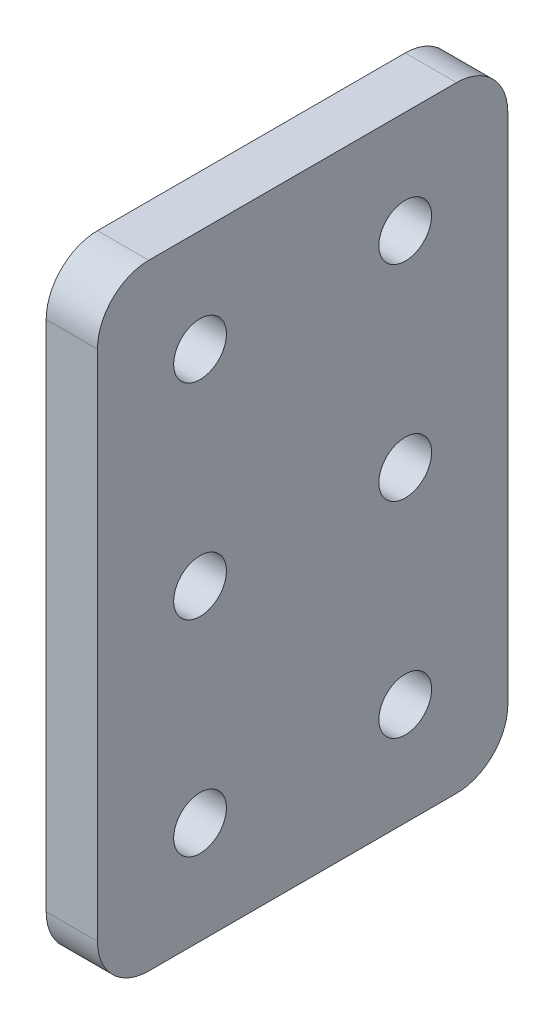
SolidWorks part; units mm, degrees
ref_plane "Front Plane" through (0, 0, 0) normal (0, 0, 1) x (1, 0, 0)
ref_plane "Top Plane" through (0, 0, 0) normal (0, 1, 0) x (1, 0, 0)
ref_plane "Right Plane" through (0, 0, 0) normal (1, 0, 0) x (0, 0, -1)
sketch "Sketch1" plane through (0, 0, 0) normal (1, 0, 0) x (0, 0, -1)
  line L0 (12.7, 63.5) -> (38.1, 63.5) construction
  line L1 (0, 0) -> (50.8, 0)
  line L2 (0, 0) -> (0, 76.2)
  line L3 (0, 76.2) -> (50.8, 76.2)
  line L4 (50.8, 0) -> (50.8, 76.2)
  line L5 (12.7, 63.5) -> (12.7, 38.1) construction
  circle A0 centre (12.7, 63.5) radius 3.2639
  circle A1 centre (38.1, 63.5) radius 3.2639
  circle A2 centre (12.7, 38.1) radius 3.2639
  circle A3 centre (38.1, 38.1) radius 3.2639
  circle A4 centre (12.7, 12.7) radius 3.2639
  circle A5 centre (38.1, 12.7) radius 3.2639
  dimension "D5" = 6.5278
  dimension "D1" = 50.8
  dimension "D2" = 76.2
  dimension "D3" = 12.7
  dimension "D4" = 12.7
  dimension "D6" = 90
  dimension "D7" = 25.4
  dimension "D8" = 12.7
  dimension "D9" = 25.4
extrude "Extrude1" add sketch "Sketch1" along normal blind 6.35
fillet "Fillet1" radius 6.35 4 edges at (3.175, 0, -50.8) (3.175, 0, 0) (3.175, 76.2, -50.8) (3.175, 76.2, 0)
